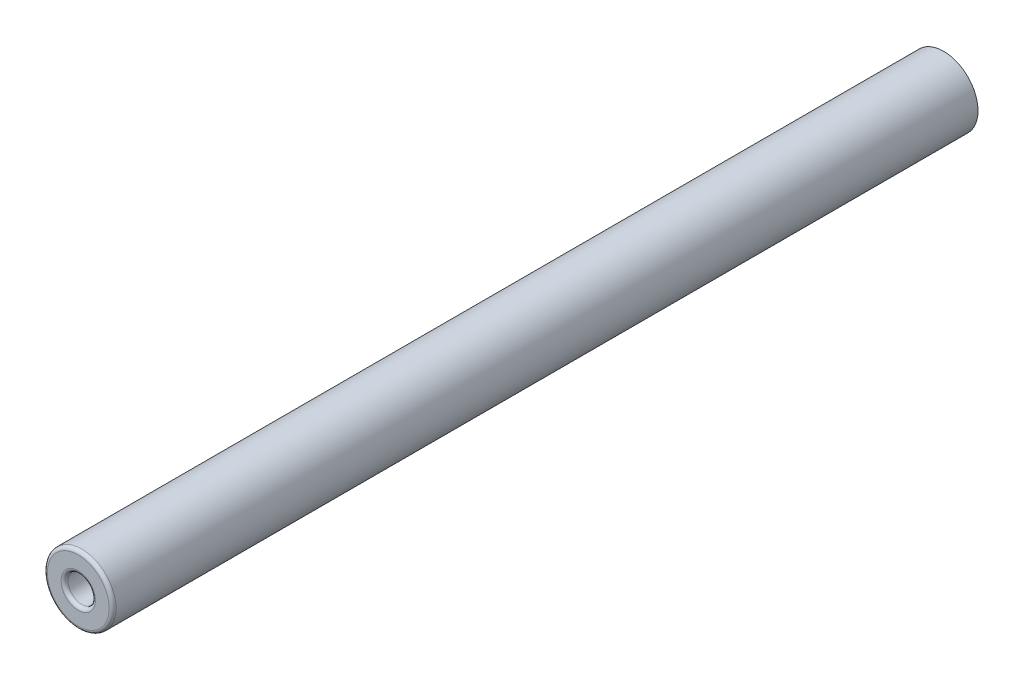
SolidWorks part; units mm, degrees
ref_plane "Front Plane" through (0, 0, 0) normal (0, 0, 1) x (1, 0, 0)
ref_plane "Top Plane" through (0, 0, 0) normal (0, 1, 0) x (1, 0, 0)
ref_plane "Right Plane" through (0, 0, 0) normal (1, 0, 0) x (0, 0, -1)
sketch "Sketch1" plane through (0, 0, 0) normal (0, 0, 1) x (1, 0, 0)
  circle A0 centre (0, 0) radius 2.5
  dimension "D1" = 5
extrude "Boss-Extrude1" add sketch "Sketch1" along normal blind 63
sketch "Sketch2" plane through (0, 0, 63) normal (0, 0, 1) x (1, 0, 0)
  circle A0 centre (0, 0) radius 1
  dimension "D1" = 2
extrude "Cut-Extrude1" cut sketch "Sketch2" against normal blind 10
fillet "Fillet1" radius 0.25 2 edges at (2.5, 0, 63) (1, 0, 63)
ref_plane "Shaft Flat" through (0, 0, 48) normal (0, 0, 1) x (1, 0, 0)
